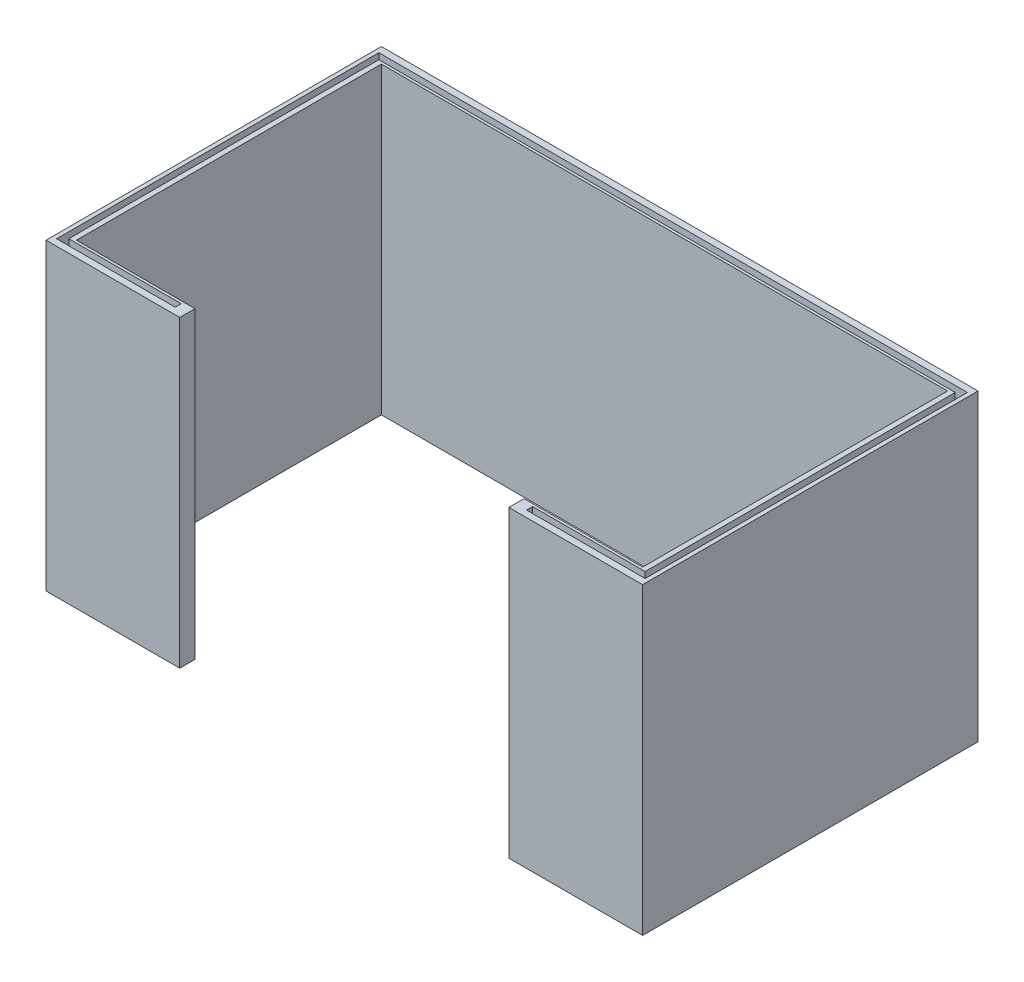
SolidWorks part; units mm, degrees
ref_plane "Front Plane" through (0, 0, 0) normal (0, 0, 1) x (1, 0, 0)
ref_plane "Top Plane" through (0, 0, 0) normal (0, 1, 0) x (1, 0, 0)
ref_plane "Right Plane" through (0, 0, 0) normal (1, 0, 0) x (0, 0, -1)
sketch "Sketch1" plane through (0, 0, 0) normal (0, 1, 0) x (1, 0, 0)
  line L0 (-32.5, -30.12) -> (-32.5, -33.12)
  line L1 (55.915, -30.12) -> (32.5, -30.12)
  line L2 (55.915, -30.12) -> (55.915, 30.12)
  line L3 (55.915, 30.12) -> (-55.915, 30.12)
  line L4 (-55.915, -30.12) -> (-55.915, 30.12)
  line L5 (55.915, -30.12) -> (-55.915, 30.12) construction
  line L6 (55.915, 30.12) -> (-55.915, -30.12) construction
  line L7 (58.915, -33.12) -> (32.5, -33.12)
  line L8 (58.915, -33.12) -> (58.915, 33.12)
  line L9 (58.915, 33.12) -> (-58.915, 33.12)
  line L10 (-58.915, -33.12) -> (-58.915, 33.12)
  line L11 (58.915, -33.12) -> (-58.915, 33.12) construction
  line L12 (58.915, 33.12) -> (-58.915, -33.12) construction
  line L13 (32.5, -30.12) -> (32.5, -33.12)
  line L14 (0, 0) -> (0, -33.12) construction
  line L15 (-32.5, -30.12) -> (-55.915, -30.12)
  line L16 (-32.5, -33.12) -> (-58.915, -33.12)
  point P0 (0, 0)
  point P6 (0, 0)
  dimension "D1" = 111.83
  dimension "D2" = 60.24
  dimension "D3" = 3
  dimension "D4" = 3
  dimension "D5" = 65
extrude "Boss-Extrude1" add sketch "Sketch1" along normal blind 60
sketch "Sketch2" plane through (0, 60, 0) normal (0, 1, 0) x (1, 0, 0)
  line L0 (-34.7, -30.62) -> (-34.7, -31.82)
  line L1 (58.115, -31.82) -> (34.7, -31.82)
  line L2 (58.115, -31.82) -> (58.115, 31.82)
  line L3 (58.115, 31.82) -> (-58.115, 31.82)
  line L4 (-58.115, -31.82) -> (-58.115, 31.82)
  line L5 (58.115, -31.82) -> (-58.115, 31.82) construction
  line L6 (58.115, 31.82) -> (-58.115, -31.82) construction
  line L7 (56.915, -30.62) -> (34.7, -30.62)
  line L8 (56.915, -30.62) -> (56.915, 30.62)
  line L9 (56.915, 30.62) -> (-56.915, 30.62)
  line L10 (-56.915, -30.62) -> (-56.915, 30.62)
  line L11 (56.915, -30.62) -> (-56.915, 30.62) construction
  line L12 (56.915, 30.62) -> (-56.915, -30.62) construction
  line L13 (58.915, -33.12) -> (-58.915, -33.12) construction
  line L14 (58.915, -33.12) -> (58.915, 33.12) construction
  line L15 (58.915, 33.12) -> (-58.915, 33.12) construction
  line L16 (-58.915, -33.12) -> (-58.915, 33.12) construction
  line L17 (58.915, -33.12) -> (-58.915, 33.12) construction
  line L18 (58.915, 33.12) -> (-58.915, -33.12) construction
  line L19 (55.915, -30.12) -> (-55.915, -30.12) construction
  line L20 (55.915, -30.12) -> (55.915, 30.12) construction
  line L21 (55.915, 30.12) -> (-55.915, 30.12) construction
  line L22 (-55.915, -30.12) -> (-55.915, 30.12) construction
  line L23 (55.915, -30.12) -> (-55.915, 30.12) construction
  line L24 (55.915, 30.12) -> (-55.915, -30.12) construction
  line L25 (34.7, -30.62) -> (34.7, -31.82)
  line L26 (-34.7, -31.82) -> (-58.115, -31.82)
  line L27 (-34.7, -30.62) -> (-56.915, -30.62)
  line L28 (-32.5, -33.12) -> (-32.5, -30.12) construction
  line L29 (32.5, -30.12) -> (32.5, -33.12) construction
  point P0 (0, 0)
  point P6 (0, 0)
  point P11 (0, 0)
  point P17 (0, 0)
  dimension "D1" = 1.2
  dimension "D2" = 1.2
  dimension "D3" = 1
  dimension "D4" = 1
  dimension "D5" = 2.2
  dimension "D6" = 2.2
extrude "Cut-Extrude1" cut sketch "Sketch2" against normal blind 5
